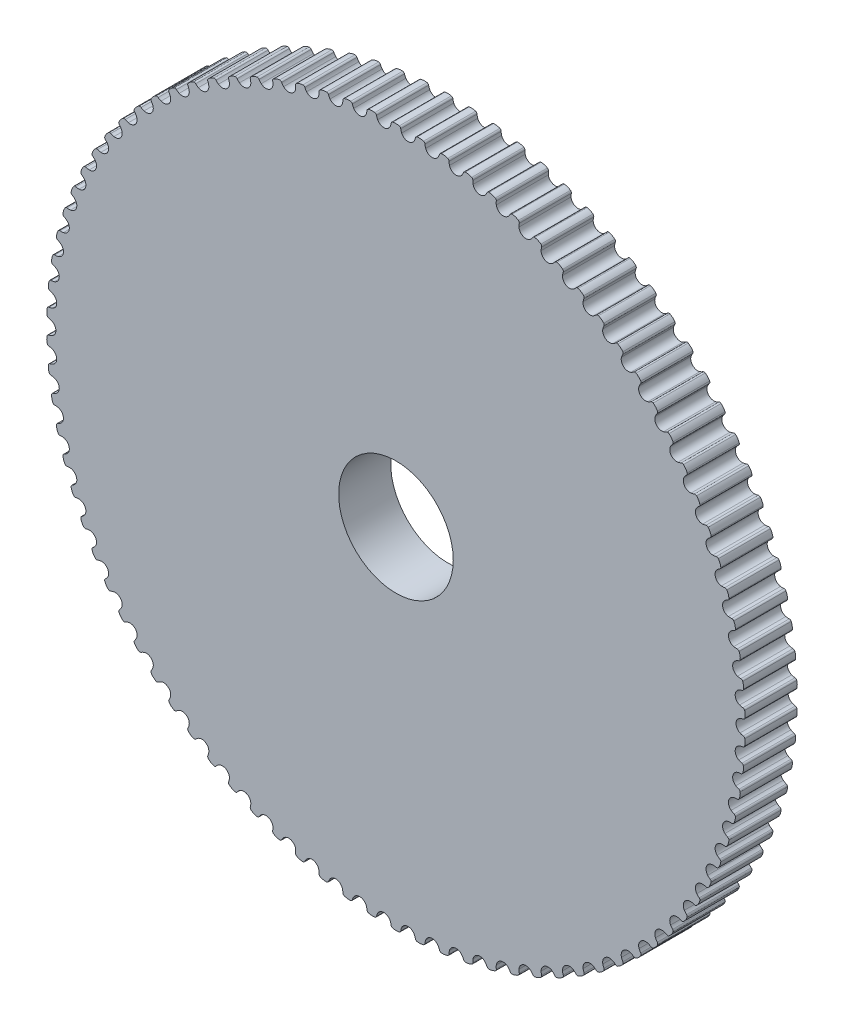
SolidWorks part; units mm, degrees
ref_plane "Front Plane" through (0, 0, 0) normal (0, 0, 1) x (1, 0, 0)
ref_plane "Top Plane" through (0, 0, 0) normal (0, 1, 0) x (1, 0, 0)
ref_plane "Right Plane" through (0, 0, 0) normal (1, 0, 0) x (0, 0, -1)
sketch "Sketch1" plane through (0, 0, 0) normal (0, 0, 1) x (1, 0, 0)
  circle A0 centre (0, 0) radius 42.9718
  dimension "D1" = 85.9437
extrude "Boss-Extrude1" add sketch "Sketch1" along normal mid plane 6.35
sketch "Tooth Profile" plane through (0, 0, 0) normal (0, 0, 1) x (1, 0, 0)
  line L0 (0, 0) -> (0, 42.9718) construction
  line L1 (1.4466, 41.4256) -> (1.4997, 42.9457) construction
  line L2 (2.1092, 42.92) -> (2.0906, 42.5425) construction
  line L3 (0, 42.5908) -> (0, 42.9718)
  circle A0 centre (0, 0) radius 42.9718 construction
  arc A1 (0.6969, 41.9358) -> (1.4466, 41.4256) centre (1.4763, 42.2751) ccw
  arc A2 (0.3977, 42.5421) -> (0, 42.5908) centre (0, 40.9438) ccw
  arc A4 (0.585, 42.3338) -> (0.6969, 41.9358) centre (2.0906, 42.5425) ccw
  arc A5 (1.4997, 42.9457) -> (2.1092, 42.92) centre (0, 0) cw construction
  arc A6 (0.3977, 42.5421) -> (0.585, 42.3338) centre (0.3374, 42.2995) cw
  arc A7 (1.4763, 42.2751) -> (0.3374, 42.2995) centre (0, 0) ccw construction
  arc A8 (0, 42.9718) -> (1.4997, 42.9457) centre (0, 0) cw
  dimension "D2" = 1.52
  dimension "D4" = 0.85
  dimension "D1" = 0.25
  dimension "D5" = 1.521
  dimension "D3" = 2
  dimension "D7" = 0.381
  dimension "D6" = 0.61
sketch "Sketch3" plane through (0, 0, 3.175) normal (0, 0, 1) x (1, 0, 0)
  line L1 (0, 42.5908) -> (0, 42.9718) construction
  line L3 (0, 42.5908) -> (0, 42.9718)
  line L4 (1.4466, 41.4256) -> (1.4997, 42.9457) construction
  line L5 (1.4466, 41.4256) -> (1.4997, 42.9457) construction
  line L6 (2.971, 42.4871) -> (2.9976, 42.8672)
  arc A10 (1.4997, 42.9457) -> (0, 42.9718) centre (0, 0) ccw construction
  arc A11 (0.3977, 42.5421) -> (0, 42.5908) centre (0, 40.9438) ccw construction
  arc A12 (0.585, 42.3338) -> (0.3977, 42.5421) centre (0.3374, 42.2995) ccw construction
  arc A13 (0.585, 42.3338) -> (0.6969, 41.9358) centre (2.0906, 42.5425) ccw construction
  arc A14 (0.6969, 41.9358) -> (1.4466, 41.4256) centre (1.4763, 42.2751) ccw construction
  arc A15 (2.9976, 42.8672) -> (0, 42.9718) centre (0, 0) ccw
  arc A16 (0.3977, 42.5421) -> (0, 42.5908) centre (0, 40.9438) ccw
  arc A17 (0.585, 42.3338) -> (0.3977, 42.5421) centre (0.3374, 42.2995) ccw
  arc A18 (0.585, 42.3338) -> (0.6969, 41.9358) centre (2.0906, 42.5425) ccw
  arc A19 (0.6969, 41.9358) -> (2.2301, 41.8823) centre (1.4763, 42.2751) ccw
  arc A20 (2.3695, 42.2715) -> (2.2301, 41.8823) centre (0.8821, 42.5847) cw
  arc A21 (2.3695, 42.2715) -> (2.5708, 42.4662) centre (2.6141, 42.22) cw
  arc A22 (2.5708, 42.4662) -> (2.971, 42.4871) centre (2.8561, 40.8441) cw
extrude "Cut-Extrude1" cut sketch "Sketch3" against normal through all both and the other way through all
pattern_circular "CirPattern1" count 90 over 360 about axis through (0, 0, 3.175) along (0, 0, -1) of "Cut-Extrude1"
hole_wizard "3/8 Clearance Hole1" positions "Sketch4" profile "Sketch5" hole size "3/8" standard "ANSI Inch" end condition through all
sketch "Sketch4" plane through (0, 0, 3.175) normal (0, 0, 1) x (1, 0, 0)
  point P0 (0, 0)
sketch "Sketch5" plane through (0, 0, 3.175) normal (1, 0, 0) x (0, -1, 0)
  line L0 (0, 0) -> (0, 6.35)
  line L1 (0, 6.35) -> (6.985, 6.35)
  line L2 (6.985, 6.35) -> (6.985, 0)
  line L5 (6.985, 0) -> (0, 0)
  line L11 (0, -6.35) -> (0, 107.95) construction
  dimension "Thru Hole Dia." = 13.97
  dimension "Thru Hole Depth" = 6.35
equation "\"n\" = 90'Number of teeth"
equation "\"p\"= 3mm'Pitch"
equation "\"pd\"= \"n\" * \"p\" / pi"
equation "\"D1@Sketch1\"=\"pd\""
equation "\"D3@Tooth Profile\" = 180 / \"n\""
equation "\"D1@CirPattern1\"=\"n\""
